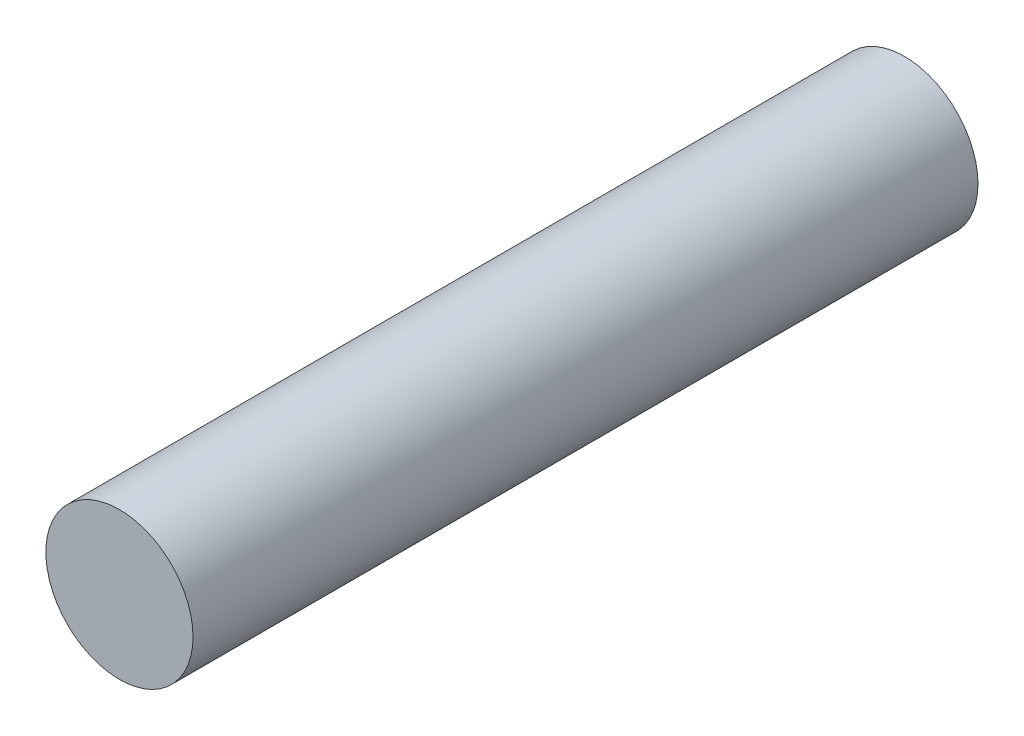
SolidWorks part; units mm, degrees
material "Plain Carbon Steel"
ref_plane "Front Plane" through (0, 0, 0) normal (0, 0, 1) x (1, 0, 0)
ref_plane "Top Plane" through (0, 0, 0) normal (0, 1, 0) x (1, 0, 0)
ref_plane "Right Plane" through (0, 0, 0) normal (1, 0, 0) x (0, 0, -1)
sketch "Sketch1" plane through (0, 0, 0) normal (0, 0, 1) x (1, 0, 0)
  circle A0 centre (0, 0) radius 19.05
  dimension "D1" = 38.1
extrude "Boss-Extrude1" add sketch "Sketch1" along normal blind 203.2
